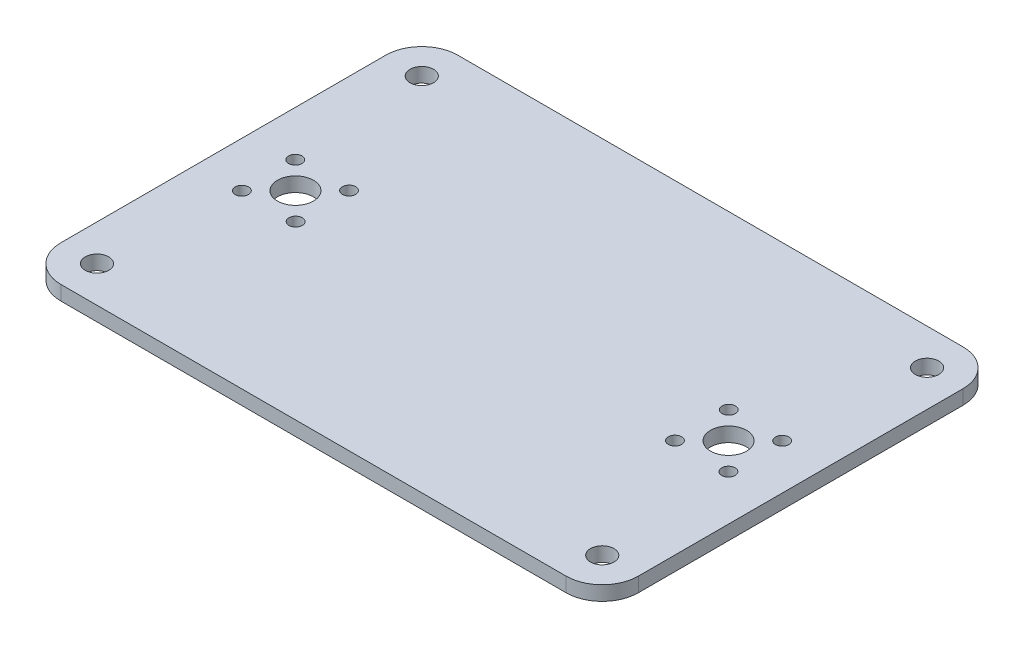
SolidWorks part; units mm, degrees
material "ABS"
ref_plane "Спереди" through (0, 0, 0) normal (0, 0, 1) x (1, 0, 0)
ref_plane "Сверху" through (0, 0, 0) normal (0, 1, 0) x (1, 0, 0)
ref_plane "Справа" through (0, 0, 0) normal (1, 0, 0) x (0, 0, -1)
sketch "Эскиз1" plane through (0, 0, 0) normal (0, 1, 0) x (1, 0, 0)
  line L0 (0, 0) -> (-95.7217, 0) construction
  line L1 (70, -55) -> (-70, -55)
  line L2 (80, -45) -> (80, 45)
  line L3 (70, 55) -> (-70, 55)
  line L4 (-80, -45) -> (-80, 45)
  line L5 (80, -55) -> (-80, 55) construction
  line L6 (80, 55) -> (-80, -55) construction
  line L7 (0, 0) -> (0, 74.6381) construction
  line L8 (-60, 0) -> (-73.6976, 13.6976) construction
  circle A0 centre (-60, 0) radius 5
  circle A1 centre (-60, 0) radius 10.5
  circle A2 centre (-67.4466, 7.4025) radius 1.85
  circle A3 centre (-52.5975, 7.4466) radius 1.85
  circle A4 centre (-52.5534, -7.4025) radius 1.85
  circle A5 centre (-67.4025, -7.4466) radius 1.85
  circle A6 centre (52.5975, 7.4466) radius 1.85
  circle A7 centre (52.5534, -7.4025) radius 1.85
  circle A8 centre (67.4025, -7.4466) radius 1.85
  circle A9 centre (60, 0) radius 5
  circle A10 centre (67.4466, 7.4025) radius 1.85
  arc A11 (-80, -45) -> (-70, -55) centre (-70, -45) ccw
  arc A12 (70, -55) -> (80, -45) centre (70, -45) ccw
  arc A13 (80, 45) -> (70, 55) centre (70, 45) ccw
  arc A14 (-70, 55) -> (-80, 45) centre (-70, 45) ccw
  circle A15 centre (-70, 45) radius 3.25
  circle A16 centre (-70, -45) radius 3.25
  circle A17 centre (70, -45) radius 3.25
  circle A18 centre (70, 45) radius 3.25
  point P0 (0, 0)
  point P24 (-60, 0)
  dimension "D4" = 10
  dimension "D5" = 21
  dimension "D6" = 3.7
  dimension "D8" = 10
  dimension "D9" = 6.5
  dimension "D1" = 110
  dimension "D2" = 160
  dimension "D3" = 20
  dimension "D7" = 4
extrude "Бобышка-Вытянуть1" add sketch "Эскиз1" along normal blind 4 contours L3 A14 L4 A11 L1 A12 L2 A13 A18 A17 A16 A15 A10 A8 A6 A5 A1 A2 A3 A4 A7 A9 | A5 A1 A4 A3 A2 A0
